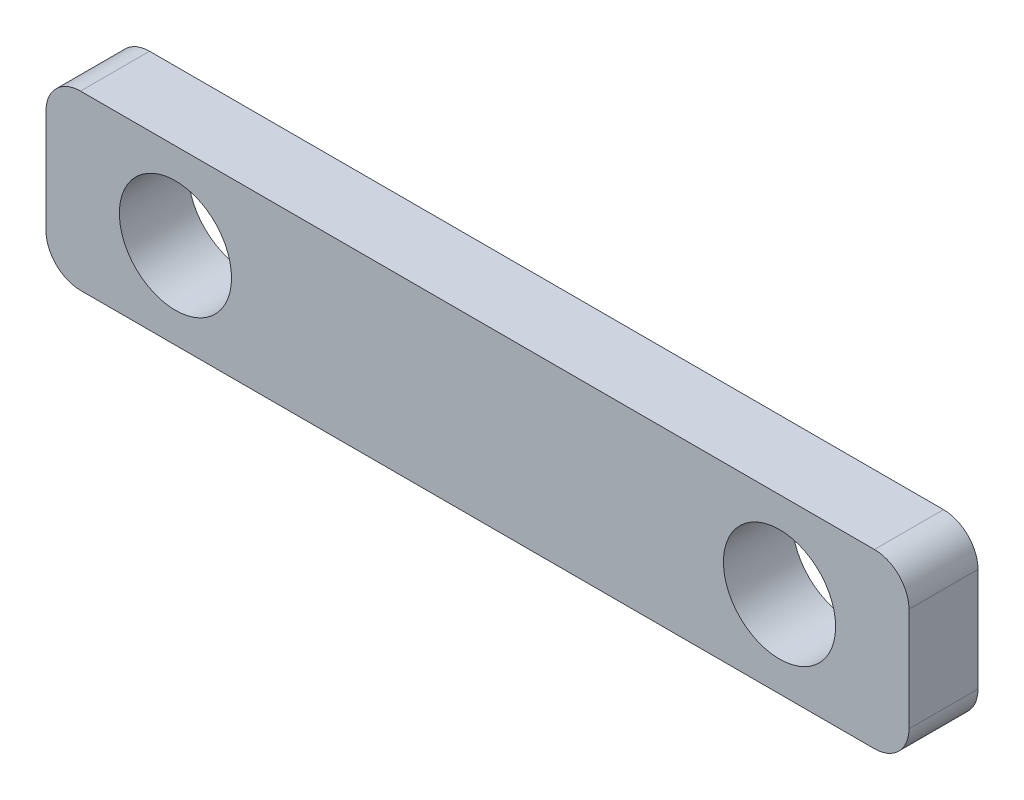
SolidWorks part; units mm, degrees
ref_plane "Face" through (0, 0, 0) normal (0, 0, 1) x (1, 0, 0)
ref_plane "Dessus" through (0, 0, 0) normal (0, 1, 0) x (1, 0, 0)
ref_plane "Droite" through (0, 0, 0) normal (1, 0, 0) x (0, 0, -1)
sketch "Esquisse1" plane through (0, 0, 0) normal (0, 0, 1) x (1, 0, 0)
  line L1 (-25, -5) -> (25, -5)
  line L2 (-25, -5) -> (-25, 5)
  line L3 (-25, 5) -> (25, 5)
  line L4 (25, -5) -> (25, 5)
  circle A0 centre (17.5, 0) radius 3.25
  circle A1 centre (-17.5, 0) radius 3.25
extrude "Boss.-Extru.1" add sketch "Esquisse1" along normal blind 4
fillet "Congé1" radius 2 4 edges at (-25, 5, 2) (25, 5, 2) (25, -5, 2) (-25, -5, 2)
